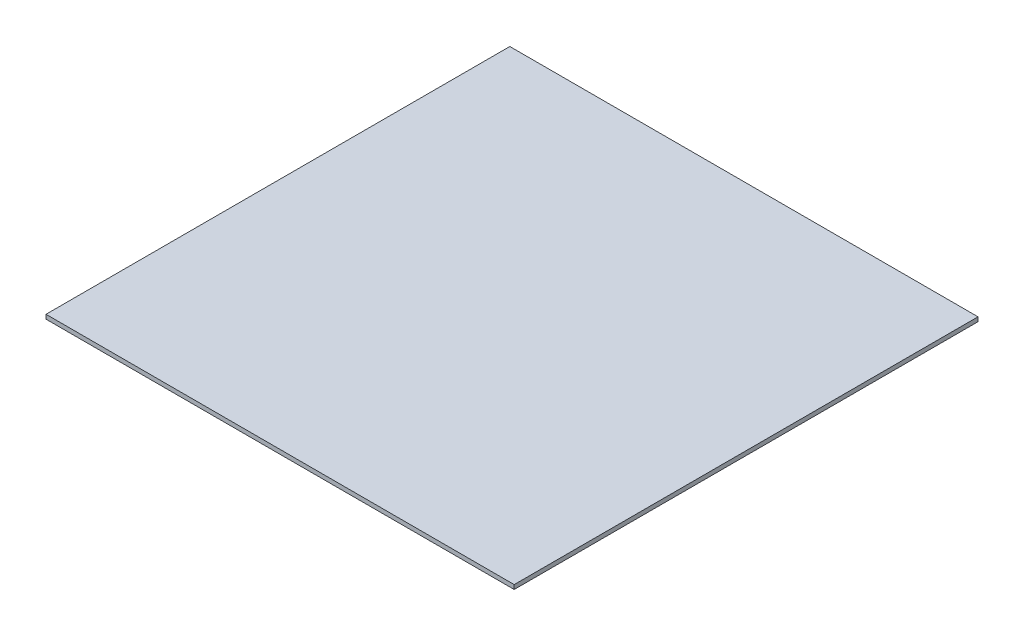
SolidWorks part; units mm, degrees
material "Oak"
ref_plane "Front Plane" through (0, 0, 0) normal (0, 0, 1) x (1, 0, 0)
ref_plane "Top Plane" through (0, 0, 0) normal (0, 1, 0) x (1, 0, 0)
ref_plane "Right Plane" through (0, 0, 0) normal (1, 0, 0) x (0, 0, -1)
sketch "Sketch1" plane through (0, 0, 0) normal (0, 1, 0) x (1, 0, 0)
  line L1 (-304.8, -301.9425) -> (304.8, -301.9425)
  line L2 (-304.8, -301.9425) -> (-304.8, 301.9425)
  line L3 (-304.8, 301.9425) -> (304.8, 301.9425)
  line L4 (304.8, -301.9425) -> (304.8, 301.9425)
  line L5 (-304.8, -301.9425) -> (304.8, 301.9425) construction
  line L6 (-304.8, 301.9425) -> (304.8, -301.9425) construction
  point P0 (0, 0)
  dimension "D1" = 609.6
  dimension "D2" = 603.885
extrude "Boss-Extrude1" add sketch "Sketch1" along normal blind 5.5562
